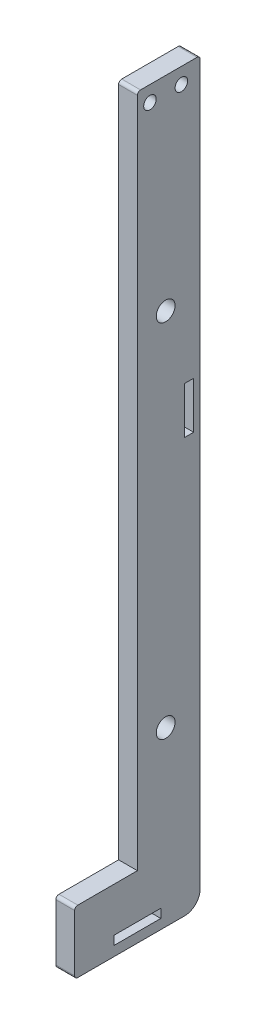
SolidWorks part; units mm, degrees
ref_plane "Спереди" through (0, 0, 0) normal (0, 0, 1) x (1, 0, 0)
ref_plane "Сверху" through (0, 0, 0) normal (0, 1, 0) x (1, 0, 0)
ref_plane "Справа" through (0, 0, 0) normal (1, 0, 0) x (0, 0, -1)
sketch "Эскиз1" plane through (0, 0, 0) normal (1, 0, 0) x (0, 0, -1)
  line L0 (0, 0) -> (-20, 0)
  line L1 (-20, 0) -> (-20, -215)
  line L2 (-20, -215) -> (-40, -215)
  line L3 (-40, -215) -> (-40, -235)
  line L4 (-40, -235) -> (0, -235)
  line L5 (0, -235) -> (0, 0)
  line L7 (-27.45, -229.095) -> (-12.55, -229.095)
  line L8 (-27.45, -229.095) -> (-27.45, -231.905)
  line L9 (-27.45, -231.905) -> (-12.55, -231.905)
  line L10 (-12.55, -229.095) -> (-12.55, -231.905)
  line L11 (-27.45, -229.095) -> (-12.55, -231.905) construction
  line L12 (-27.45, -231.905) -> (-12.55, -229.095) construction
  line L13 (-4.915, -88.05) -> (-2.085, -88.05)
  line L14 (-4.915, -88.05) -> (-4.915, -102.95)
  line L15 (-4.915, -102.95) -> (-2.085, -102.95)
  line L16 (-2.085, -88.05) -> (-2.085, -102.95)
  line L17 (-4.915, -88.05) -> (-2.085, -102.95) construction
  line L18 (-4.915, -102.95) -> (-2.085, -88.05) construction
  circle A0 centre (-16, -5) radius 2
  circle A1 centre (-6, -5) radius 2
  circle A2 centre (-11, -65) radius 3
  circle A3 centre (-11, -180) radius 3
  point P11 (-20, -230.5)
  point P20 (-3.5, -95.5)
  dimension "D8" = 4
  dimension "D9" = 6
  dimension "D1" = 20
  dimension "D2" = 35
  dimension "D3" = 20
  dimension "D4" = 40
  dimension "D5" = 10
  dimension "D6" = 4
  dimension "D7" = 5
  dimension "D10" = 65
  dimension "D11" = 11
  dimension "D13" = 115
  dimension "D14" = 2.81
  dimension "D15" = 14.9
  dimension "D16" = 4.5
  dimension "D17" = 20
  dimension "D18" = 2.83
  dimension "D19" = 14.9
  dimension "D20" = 3.5
  dimension "D21" = 30.5
  dimension "D12" = 2
extrude "Бобышка-Вытянуть1" add sketch "Эскиз1" along normal blind 6 contours L4 L5 L0 L1 L2 L3 A2 A1 A0
fillet "Скругление1" radius 1 4 edges at (3, 0, 0) (3, 0, 20) (3, -215, 40) (3, -235, 40)
fillet "Скругление2" radius 5 1 edges at (3, -235, 0)
